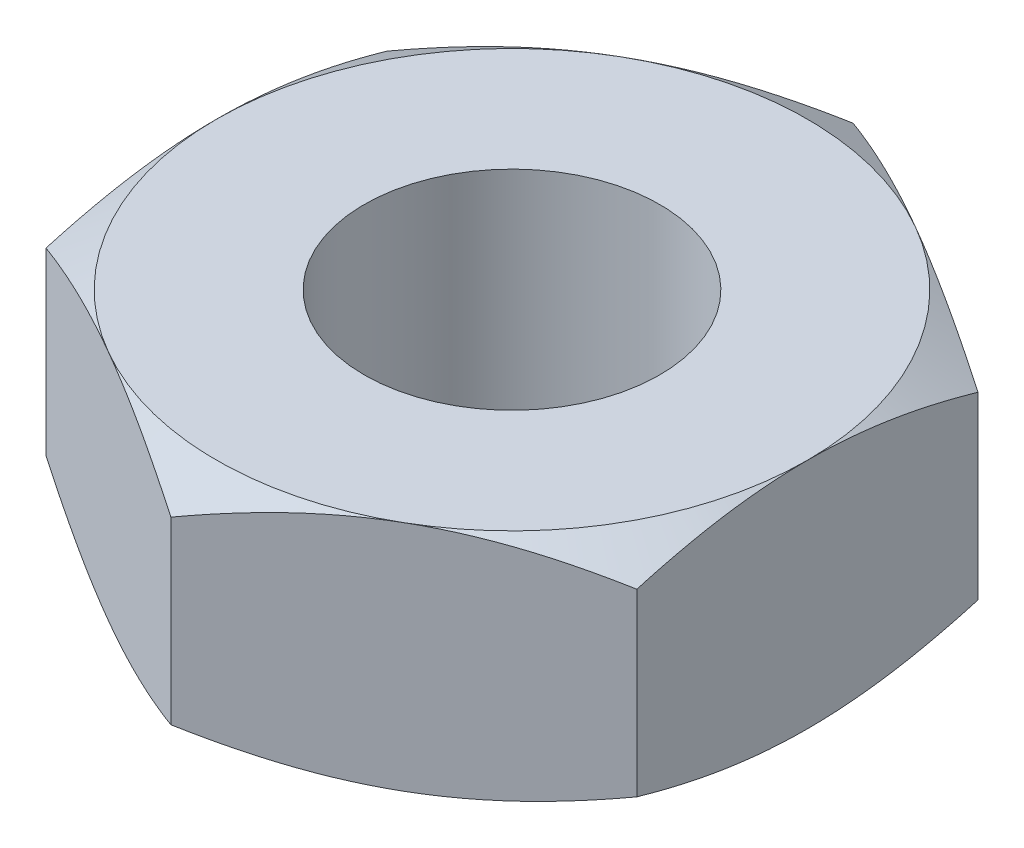
SolidWorks part; units mm, degrees
ref_plane "Front Plane" through (0, 0, 0) normal (0, 0, 1) x (1, 0, 0)
ref_plane "Top Plane" through (0, 0, 0) normal (0, 1, 0) x (1, 0, 0)
ref_plane "Right Plane" through (0, 0, 0) normal (1, 0, 0) x (0, 0, -1)
sketch "Sketch1" plane through (0, 0, 0) normal (0, 1, 0) x (1, 0, 0)
  line L1 (12.7, 7.3323) -> (0, 14.6647)
  line L2 (0, 14.6647) -> (-12.7, 7.3323)
  line L3 (-12.7, 7.3323) -> (-12.7, -7.3323)
  line L4 (-12.7, -7.3323) -> (0, -14.6647)
  line L5 (0, -14.6647) -> (12.7, -7.3323)
  line L6 (12.7, -7.3323) -> (12.7, 7.3323)
  circle A0 centre (0, 0) radius 12.7 construction
  circle A1 centre (0, 0) radius 6.35
  dimension "D2" = 12.7
  dimension "D1" = 25.4
extrude "Boss-Extrude1" add sketch "Sketch1" along normal mid plane 10
cosmetic thread "Cosmetic Thread1" parameters "D2"=16
sketch "Sketch2" plane through (0, 0, 0) normal (0, 0, 1) x (1, 0, 0)
  line L0 (0, 0) -> (0, 50000) construction
  line L1 (0, 5) -> (0, -5) construction
  line L2 (0, 0) -> (50000, 0) construction
  line L3 (12.7, 5) -> (15.7, 5)
  line L4 (12.7, -5) -> (15.7, -5)
  line L5 (15.7, 5) -> (15.7, 3.2679)
  line L6 (15.7, -5) -> (15.7, -3.2679)
  line L7 (15.7, 3.2679) -> (12.7, 5)
  line L8 (15.7, -3.2679) -> (12.7, -5)
  point P4 (0, 0)
  dimension "D1" = 30
  dimension "D2" = 3
revolve "Cut-Revolve1" cut sketch "Sketch2" angle 360 about L0
